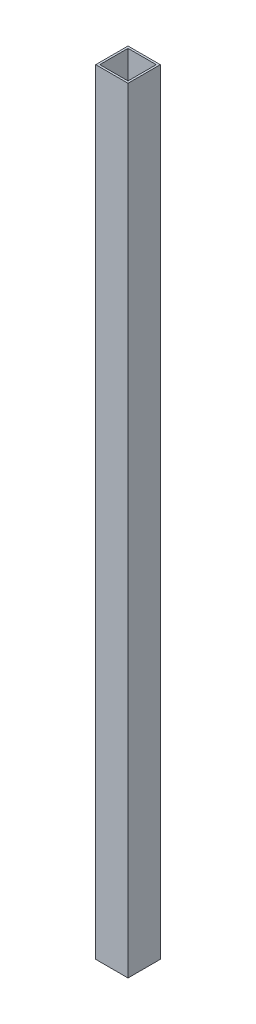
SolidWorks part; units mm, degrees
material "6061 Alloy"
ref_plane "Front Plane" through (0, 0, 0) normal (0, 0, 1) x (1, 0, 0)
ref_plane "Top Plane" through (0, 0, 0) normal (0, 1, 0) x (1, 0, 0)
ref_plane "Right Plane" through (0, 0, 0) normal (1, 0, 0) x (0, 0, -1)
sketch "Sketch1" plane through (0, 0, 0) normal (0, 1, 0) x (1, 0, 0)
  line L1 (-11.1125, -11.1125) -> (11.1125, -11.1125)
  line L2 (-11.1125, -11.1125) -> (-11.1125, 11.1125)
  line L3 (-11.1125, 11.1125) -> (11.1125, 11.1125)
  line L4 (11.1125, -11.1125) -> (11.1125, 11.1125)
  line L5 (-11.1125, -11.1125) -> (11.1125, 11.1125) construction
  line L6 (-11.1125, 11.1125) -> (11.1125, -11.1125) construction
  line L7 (-12.7, -12.7) -> (12.7, -12.7)
  line L8 (-12.7, -12.7) -> (-12.7, 12.7)
  line L9 (-12.7, 12.7) -> (12.7, 12.7)
  line L10 (12.7, -12.7) -> (12.7, 12.7)
  line L11 (-12.7, -12.7) -> (12.7, 12.7) construction
  line L12 (-12.7, 12.7) -> (12.7, -12.7) construction
  point P0 (0, 0)
  point P6 (0, 0)
  dimension "D1" = 25.4
  dimension "D2" = 1.5875
extrude "Boss-Extrude1" add sketch "Sketch1" along normal blind 609.6
